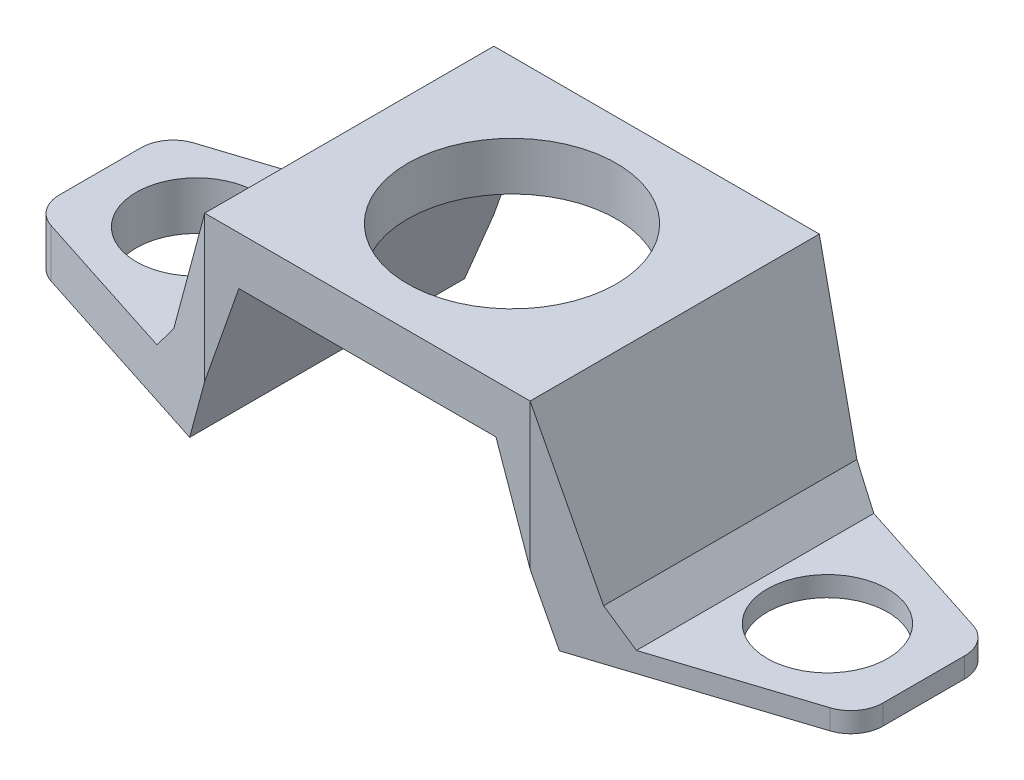
SolidWorks part; units mm, degrees
material "ABS"
ref_plane "Front Plane" through (0, 0, 0) normal (0, 0, 1) x (1, 0, 0)
ref_plane "Top Plane" through (0, 0, 0) normal (0, 1, 0) x (1, 0, 0)
ref_plane "Right Plane" through (0, 0, 0) normal (1, 0, 0) x (0, 0, -1)
sketch "Sketch1" plane through (0, 0, 0) normal (0, 0, 1) x (1, 0, 0)
  line L0 (-25.6336, 0) -> (-11.5064, 0)
  line L1 (-11.5064, 0) -> (-8, 10)
  line L2 (-8, 10) -> (0, 10)
  line L3 (0, 0) -> (0, 30.9357) construction
  line L4 (-18.57, 0) -> (-18.57, 10.0457) construction
  line L5 (-25.6336, 3) -> (-13.6336, 3)
  line L6 (-13.6336, 3) -> (-10.1272, 13)
  line L7 (-10.1272, 13) -> (0, 13)
  line L8 (-25.6336, 3) -> (-25.6336, 0)
  line L9 (10.1272, 13) -> (0, 13)
  line L10 (8, 10) -> (0, 10)
  line L11 (18.57, 0) -> (18.57, 10.0457) construction
  line L12 (25.6336, 3) -> (25.6336, 0)
  line L13 (13.6336, 3) -> (10.1272, 13)
  line L14 (25.6336, 3) -> (13.6336, 3)
  line L15 (11.5064, 0) -> (8, 10)
  line L16 (25.6336, 0) -> (11.5064, 0)
  dimension "D1" = 18.57
  dimension "D2" = 10
  dimension "D3" = 8
  dimension "D4" = 12
  dimension "D5" = 3
extrude "Boss-Extrude1" add sketch "Sketch1" along normal mid plane 18
sketch "Sketch2" plane through (0, 13, 0) normal (0, 1, 0) x (1, 0, 0)
  circle A0 centre (0, 0) radius 6.5
  dimension "D1" = 13
extrude "Cut-Extrude1" cut sketch "Sketch2" against normal up to next
sketch "Sketch3" plane through (0, 13, 0) normal (0, 1, 0) x (1, 0, 0)
  line L0 (-10.1272, 9) -> (-25.6336, 4)
  line L1 (-25.6336, -9) -> (-25.6336, 9) construction
  line L2 (-25.6336, 4) -> (-25.6336, 9)
  line L3 (-13.6336, 9) -> (-25.6336, 9) construction
  line L4 (-25.6336, 9) -> (-10.1272, 9)
  line L5 (-25.6336, 0) -> (0, 0) construction
  line L6 (0, 0) -> (0, 9) construction
  line L7 (10.1272, 9) -> (-10.1272, 9) construction
  line L8 (-10.1272, -9) -> (-25.6336, -4)
  line L9 (-25.6336, -9) -> (-10.1272, -9)
  line L10 (-25.6336, -4) -> (-25.6336, -9)
  line L11 (25.6336, 9) -> (10.1272, 9)
  line L12 (25.6336, 4) -> (25.6336, 9)
  line L13 (10.1272, 9) -> (25.6336, 4)
  line L14 (25.6336, -4) -> (25.6336, -9)
  line L15 (25.6336, -9) -> (10.1272, -9)
  line L16 (10.1272, -9) -> (25.6336, -4)
  dimension "D1" = 4
extrude "Cut-Extrude2" cut sketch "Sketch3" against normal blind 18
sketch "Sketch4" plane through (0, 3, 0) normal (0, 1, 0) x (1, 0, 0)
  line L0 (0, 0) -> (-50000, 0) construction
  line L1 (-25.6336, -4) -> (-25.6336, 4) construction
  line L3 (25.6336, -4) -> (25.6336, 4) construction
  circle A0 centre (-19.6336, 0) radius 3.75
  circle A1 centre (19.6336, 0) radius 3.75
  dimension "D3" = 7.5
  dimension "D1" = 6
  dimension "D2" = 6
extrude "Cut-Extrude3" cut sketch "Sketch4" against normal up to next
sketch "Sketch5" plane through (0, 0, 0) normal (0, 0, 1) x (1, 0, 0)
  line L0 (13.6336, 3) -> (14.2472, 1.25)
  line L1 (14.2472, 1.25) -> (25.6336, 1.25)
  line L2 (25.6336, 0) -> (25.6336, 3) construction
  line L3 (25.6336, 1.25) -> (25.6336, 3)
  line L4 (25.6336, 3) -> (13.6336, 3)
  line L5 (10.1272, 13) -> (13.6336, 3) construction
  dimension "D1" = 1.75
extrude "Cut-Extrude4" cut sketch "Sketch5" against normal mid plane 20
fillet "Fillet1" radius 2 4 edges at (25.6336, 0.625, -4) (25.6336, 0.625, 4) (-25.6336, 1.5, -4) (-25.6336, 1.5, 4)
chamfer "Chamfer1" distance 2 angle 20 2 edges at (14.2472, 1.25, 0) (-13.6336, 3, 0)
